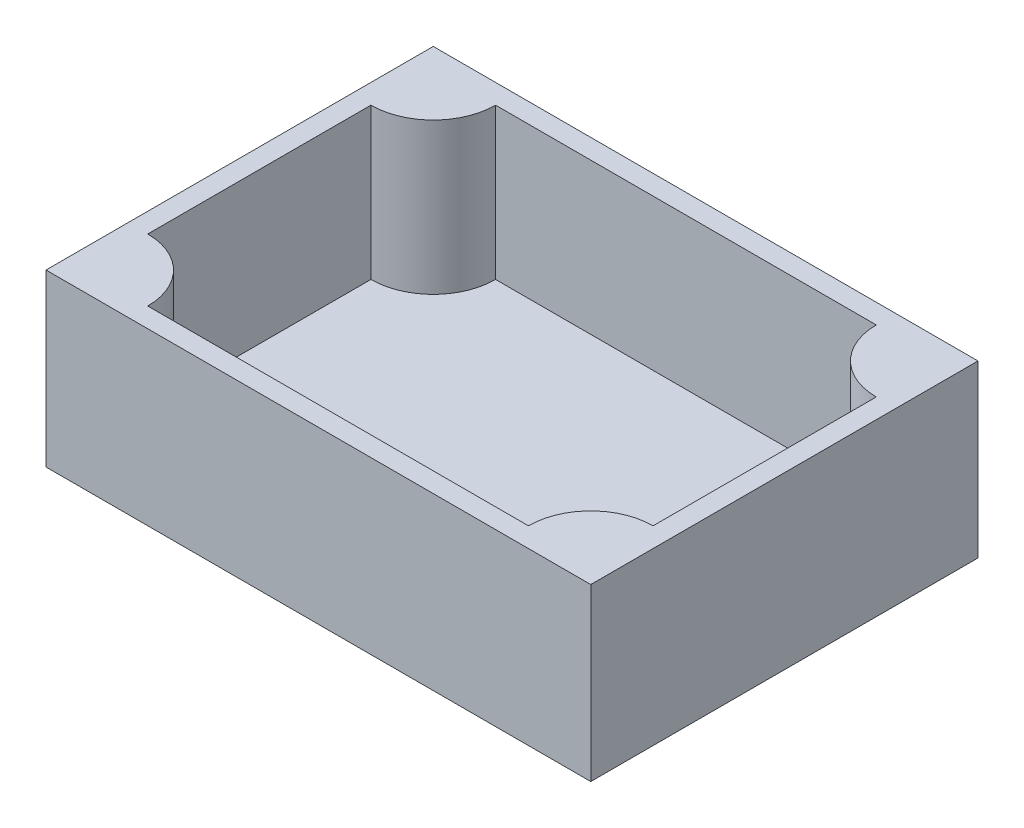
SolidWorks part; units mm, degrees
ref_plane "Front Plane" through (0, 0, 0) normal (0, 0, 1) x (1, 0, 0)
ref_plane "Top Plane" through (0, 0, 0) normal (0, 1, 0) x (1, 0, 0)
ref_plane "Right Plane" through (0, 0, 0) normal (1, 0, 0) x (0, 0, -1)
sketch "Sketch1" plane through (0, 0, 0) normal (0, 1, 0) x (1, 0, 0)
  line L1 (0, 0) -> (83, 0)
  line L2 (0, 0) -> (0, 59)
  line L3 (0, 59) -> (83, 59)
  line L4 (83, 0) -> (83, 59)
  dimension "D1" = 59
  dimension "D2" = 83
extrude "Boss-Extrude1" add sketch "Sketch1" along normal blind 3
sketch "Sketch2" plane through (0, 3, 0) normal (0, 1, 0) x (1, 0, 0)
  line L9 (0, 0) -> (0, 59)
  line L10 (0, 29.5) -> (3, 29.5) construction
  line L11 (3, 46.5) -> (3, 12.5)
  line L13 (0, 59) -> (0, 0) construction
  line L14 (0, 0) -> (83, 0) construction
  line L18 (12.5, 3) -> (70.5, 3)
  line L19 (41.5, 3) -> (41.5, 0) construction
  line L24 (83, 0) -> (0, 0)
  line L25 (41.5, 56) -> (41.5, 59) construction
  line L26 (83, 59) -> (0, 59)
  line L27 (12.5, 56) -> (70.5, 56)
  line L29 (83, 29.5) -> (80, 29.5) construction
  line L32 (80, 46.5) -> (80, 12.5)
  line L33 (83, 0) -> (83, 59)
  line L34 (7.75, 51.25) -> (7.75, 7.75) construction
  line L35 (7.75, 3) -> (12.5, 3) construction
  line L36 (3, 56) -> (7.75, 56) construction
  line L37 (3, 56) -> (3, 51.25) construction
  line L38 (3, 51.25) -> (7.75, 51.25) construction
  line L39 (7.75, 56) -> (7.75, 51.25) construction
  line L40 (3, 3) -> (7.75, 3) construction
  line L41 (3, 3) -> (3, 7.75) construction
  line L42 (3, 7.75) -> (7.75, 7.75) construction
  line L43 (7.75, 3) -> (7.75, 7.75) construction
  arc A4 (3, 12.5) -> (12.5, 3) centre (3, 3) cw
  arc A5 (3, 46.5) -> (12.5, 56) centre (3, 56) ccw
  arc A6 (80, 46.5) -> (70.5, 56) centre (80, 56) cw
  arc A7 (80, 12.5) -> (70.5, 3) centre (80, 3) ccw
  point P21 (0, 29.5)
  point P24 (41.5, 0)
  dimension "D1" = 3
  dimension "D2" = 43.5
extrude "Boss-Extrude2" add sketch "Sketch2" along direction (0, -1, 0) on the side of the normal offset from surface (23 mm away) 26
